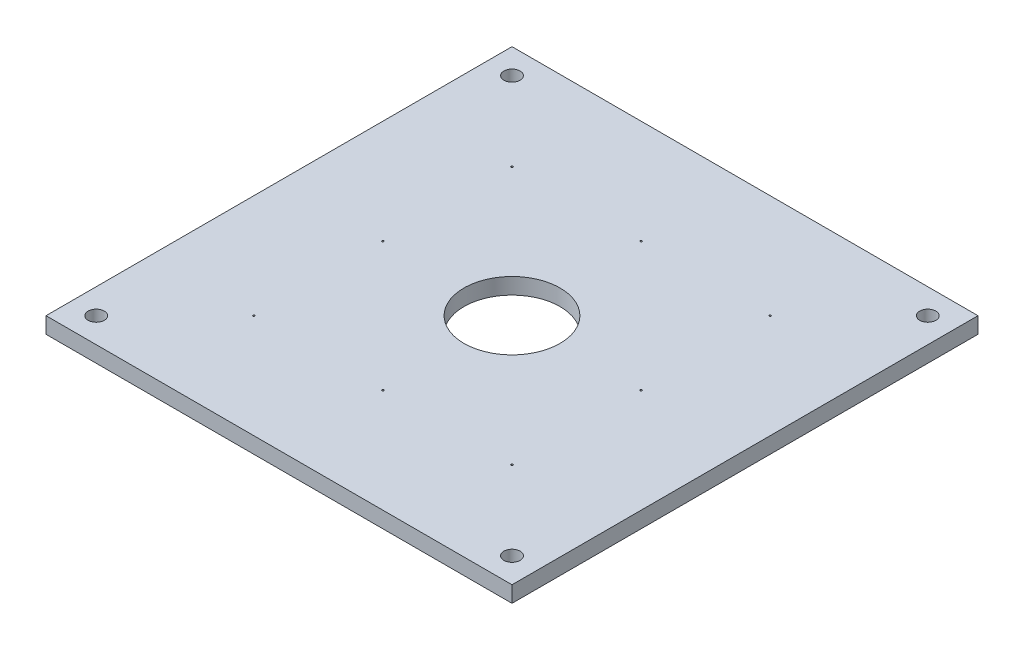
SolidWorks part; units mm, degrees
ref_plane "Front Plane" through (0, 0, 0) normal (0, 0, 1) x (1, 0, 0)
ref_plane "Top Plane" through (0, 0, 0) normal (0, 1, 0) x (1, 0, 0)
ref_plane "Right Plane" through (0, 0, 0) normal (1, 0, 0) x (0, 0, -1)
sketch "Sketch1" plane through (0, 0, 0) normal (0, 1, 0) x (1, 0, 0)
  line L1 (0, 0) -> (130, 0)
  line L2 (0, 0) -> (0, 130)
  line L3 (0, 130) -> (130, 130)
  line L4 (130, 0) -> (130, 130)
  circle A0 centre (65, 65) radius 13.4
  circle A1 centre (123, 123) radius 2.25
  circle A2 centre (65, 65) radius 59.6241 construction
  circle A3 centre (123, 7) radius 2.25
  circle A4 centre (7, 7) radius 2.25
  circle A5 centre (7, 123) radius 2.25
  dimension "D3" = 26.8
  dimension "D4" = 4.5
  dimension "D1" = 130
  dimension "D2" = 130
  dimension "D5" = 7
  dimension "D6" = 7
  dimension "D7" = 65
  dimension "D8" = 65
  dimension "D9" = 4
extrude "Boss-Extrude1" add sketch "Sketch1" along normal blind 4.5
sketch "Sketch2" plane through (0, 0, 0) normal (0, -1, 0) x (1, 0, 0)
  line L0 (65, -130) -> (65, 0) construction
  line L1 (130, -130) -> (0, -130) construction
  line L2 (0, 0) -> (130, 0) construction
  line L3 (0, -65) -> (130, -65) construction
  line L4 (0, -130) -> (0, 0) construction
  line L5 (130, 0) -> (130, -130) construction
  circle A0 centre (29, -65) radius 0.25
  circle A1 centre (65, -29) radius 0.25
  circle A2 centre (101, -65) radius 0.25
  circle A3 centre (65, -101) radius 0.25
  circle A4 centre (101, -29) radius 0.25
  circle A5 centre (29, -29) radius 0.25
  circle A6 centre (101, -101) radius 0.25
  circle A7 centre (29, -101) radius 0.25
  point P14 (65, -65)
  dimension "D2" = 0.5
  dimension "D1" = 36
  dimension "D4" = 2
  dimension "D5" = 2
  dimension "D3" = 4
extrude "Cut-Extrude1" cut sketch "Sketch2" against normal through all
equation "\"D1@Boss-Extrude1\"=\"mat@v5.assembly\""
